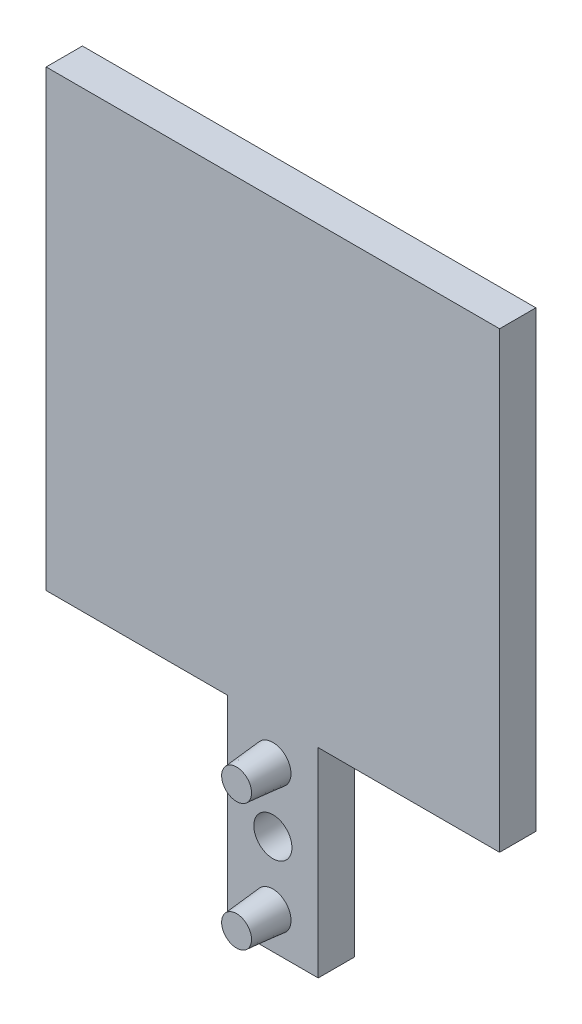
SolidWorks part; units mm, degrees
ref_plane "Front Plane" through (0, 0, 0) normal (0, 0, 1) x (1, 0, 0)
ref_plane "Top Plane" through (0, 0, 0) normal (0, 1, 0) x (1, 0, 0)
ref_plane "Right Plane" through (0, 0, 0) normal (1, 0, 0) x (0, 0, -1)
sketch "Sketch1" plane through (0, 0, 0) normal (0, 0, 1) x (1, 0, 0)
  line L0 (25, 50) -> (25, -56.8436) construction
  line L1 (0, 0) -> (20, 0)
  line L2 (0, 0) -> (0, 50)
  line L3 (0, 50) -> (50, 50)
  line L4 (50, 0) -> (50, 50)
  line L5 (30, 0) -> (50, 0)
  line L7 (20, 0) -> (20, -22)
  line L8 (20, -22) -> (30, -22)
  line L9 (30, 0) -> (30, -22)
  point P11 (25, -22)
  dimension "D1" = 50
  dimension "D2" = 50
  dimension "D3" = 10
  dimension "D4" = 22
extrude "Boss-Extrude1" add sketch "Sketch1" along normal blind 4
sketch "Sketch2" plane through (0, 0, 4) normal (0, 0, 1) x (1, 0, 0)
  line L0 (25, -22) -> (25, 50) construction
  line L1 (20, -22) -> (30, -22) construction
  line L2 (50, 50) -> (0, 50) construction
  circle A0 centre (25, -18) radius 2
  circle A2 centre (25, -4) radius 2
  dimension "D1" = 4
  dimension "D2" = 4
  dimension "D3" = 14
  dimension "D4" = 4
extrude "Boss-Extrude2" add sketch "Sketch2" along normal blind 4 draft 5
sketch "Sketch3" plane through (0, 0, 4) normal (0, 0, 1) x (1, 0, 0)
  line L0 (25, -22) -> (25, 0) construction
  line L1 (20, -22) -> (30, -22) construction
  circle A0 centre (25, -11) radius 2.1
  circle A1 centre (25, -18) radius 2 construction
  dimension "D1" = 4.2
  dimension "D2" = 7
extrude "Cut-Extrude1" cut sketch "Sketch3" against normal blind 4
